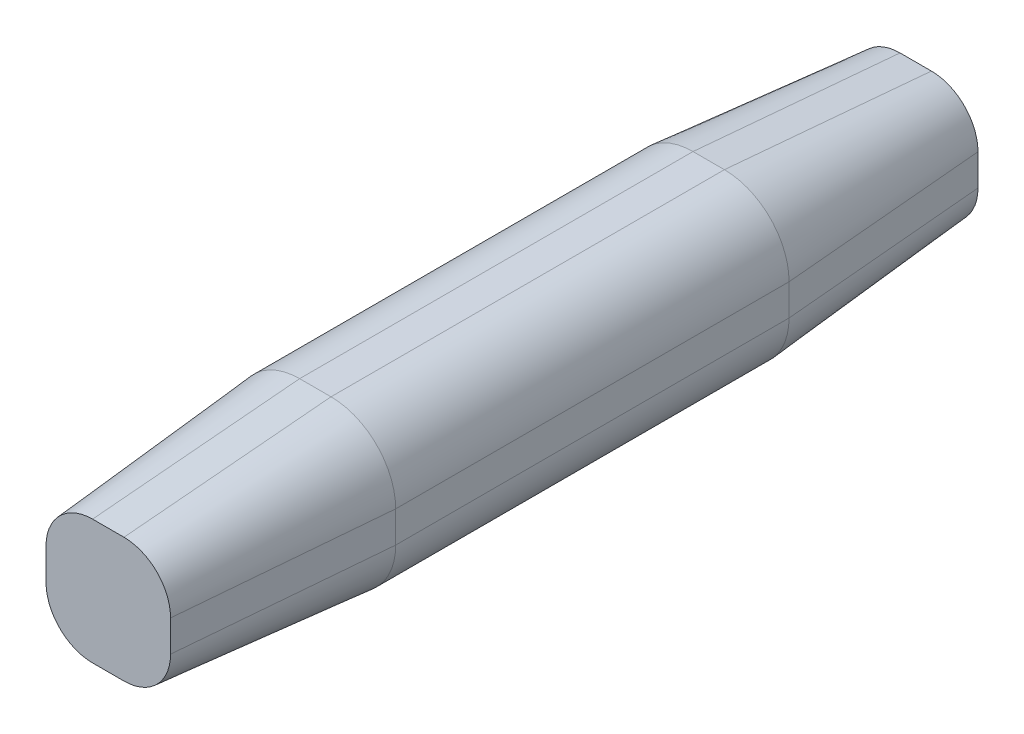
SolidWorks part; units mm, degrees
material "Bambu PAHT-CF"
ref_plane "Front Plane" through (0, 0, 0) normal (0, 0, 1) x (1, 0, 0)
ref_plane "Top Plane" through (0, 0, 0) normal (0, 1, 0) x (1, 0, 0)
ref_plane "Right Plane" through (0, 0, 0) normal (1, 0, 0) x (0, 0, -1)
sketch "Sketch1" plane through (0, 0, 0) normal (0, 0, 1) x (1, 0, 0)
  line L1 (-0.385, -1.9725) -> (0.385, -1.9725)
  line L2 (-1.9725, -0.385) -> (-1.9725, 0.385)
  line L3 (-0.385, 1.9725) -> (0.385, 1.9725)
  line L4 (1.9725, -0.385) -> (1.9725, 0.385)
  line L5 (-1.9725, -1.9725) -> (1.9725, 1.9725) construction
  line L6 (-1.9725, 1.9725) -> (1.9725, -1.9725) construction
  arc A0 (0.385, -1.9725) -> (1.9725, -0.385) centre (0.385, -0.385) ccw
  arc A1 (-0.385, -1.9725) -> (-1.9725, -0.385) centre (-0.385, -0.385) cw
  arc A2 (0.385, 1.9725) -> (1.9725, 0.385) centre (0.385, 0.385) cw
  arc A3 (-1.9725, 0.385) -> (-0.385, 1.9725) centre (-0.385, 0.385) cw
  point P0 (0, 0)
  dimension "D3" = 1.5875
  dimension "D1" = 3.945
  dimension "D2" = 3.945
extrude "Boss-Extrude1" add sketch "Sketch1" along normal blind 4.826
sketch "Sketch2" plane through (0, 0, 4.826) normal (0, 0, 1) x (1, 0, 0)
  line L4 (1.9725, -0.385) -> (1.9725, 0.385)
  line L5 (0.385, 1.9725) -> (-0.385, 1.9725)
  line L6 (-1.9725, 0.385) -> (-1.9725, -0.385)
  line L7 (-0.385, -1.9725) -> (0.385, -1.9725)
  line L8 (1.9725, -0.385) -> (1.9725, 0.385)
  line L9 (0.385, 1.9725) -> (-0.385, 1.9725)
  line L10 (-1.9725, 0.385) -> (-1.9725, -0.385)
  line L11 (-0.385, -1.9725) -> (0.385, -1.9725)
  arc A4 (0.385, -1.9725) -> (1.9725, -0.385) centre (0.385, -0.385) ccw
  arc A5 (1.9725, 0.385) -> (0.385, 1.9725) centre (0.385, 0.385) ccw
  arc A6 (-0.385, 1.9725) -> (-1.9725, 0.385) centre (-0.385, 0.385) ccw
  arc A7 (-1.9725, -0.385) -> (-0.385, -1.9725) centre (-0.385, -0.385) ccw
  arc A8 (0.385, -1.9725) -> (1.9725, -0.385) centre (0.385, -0.385) ccw
  arc A9 (1.9725, 0.385) -> (0.385, 1.9725) centre (0.385, 0.385) ccw
  arc A10 (-0.385, 1.9725) -> (-1.9725, 0.385) centre (-0.385, 0.385) ccw
  arc A11 (-1.9725, -0.385) -> (-0.385, -1.9725) centre (-0.385, -0.385) ccw
  dimension "D1" = 0
extrude "Boss-Extrude2" add sketch "Sketch2" along normal blind 5.08 draft 5
mirror "Mirror1" about plane through (0, 0, 0) normal (0, 0, 1) of "Boss-Extrude2", "Boss-Extrude1"
